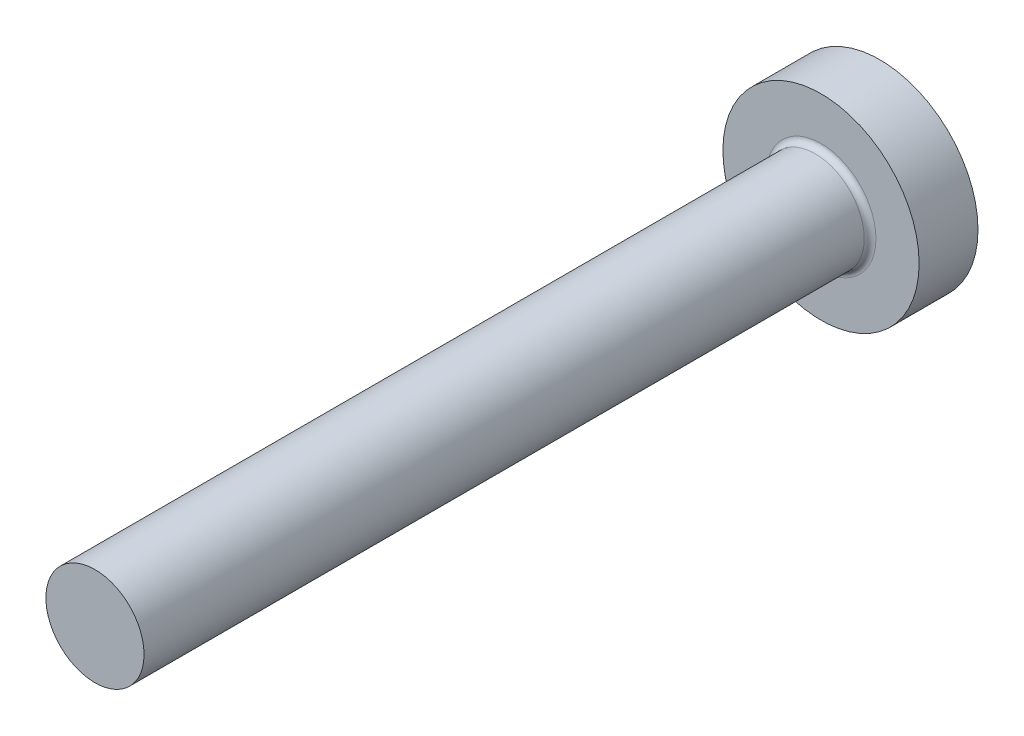
SolidWorks part; units mm, degrees
material "Legierter Stahl"
ref_plane "Vorne" through (0, 0, 0) normal (0, 0, 1) x (1, 0, 0)
ref_plane "Oben" through (0, 0, 0) normal (0, 1, 0) x (1, 0, 0)
ref_plane "Rechts" through (0, 0, 0) normal (1, 0, 0) x (0, 0, -1)
sketch "Skizze1" plane through (0, 0, 0) normal (1, 0, 0) x (0, 0, -1)
  line L0 (0, 0) -> (2.9643, 0) construction
  line L1 (0, 0) -> (0, 5)
  line L3 (-3.3, 2.5) -> (-40, 2.5)
  line L4 (-40, 2.5) -> (-40, 0)
  line L5 (0, 0) -> (-40, 0)
  line L6 (0, 5) -> (-3, 5)
  line L7 (-3, 5) -> (-3, 2.8)
  arc A0 (-3, 2.8) -> (-3.3, 2.5) centre (-3.3, 2.8) cw
  point P10 (-3, 2.5)
revolve "Basis-Rotation" add sketch "Skizze1" angle 360 about L0
